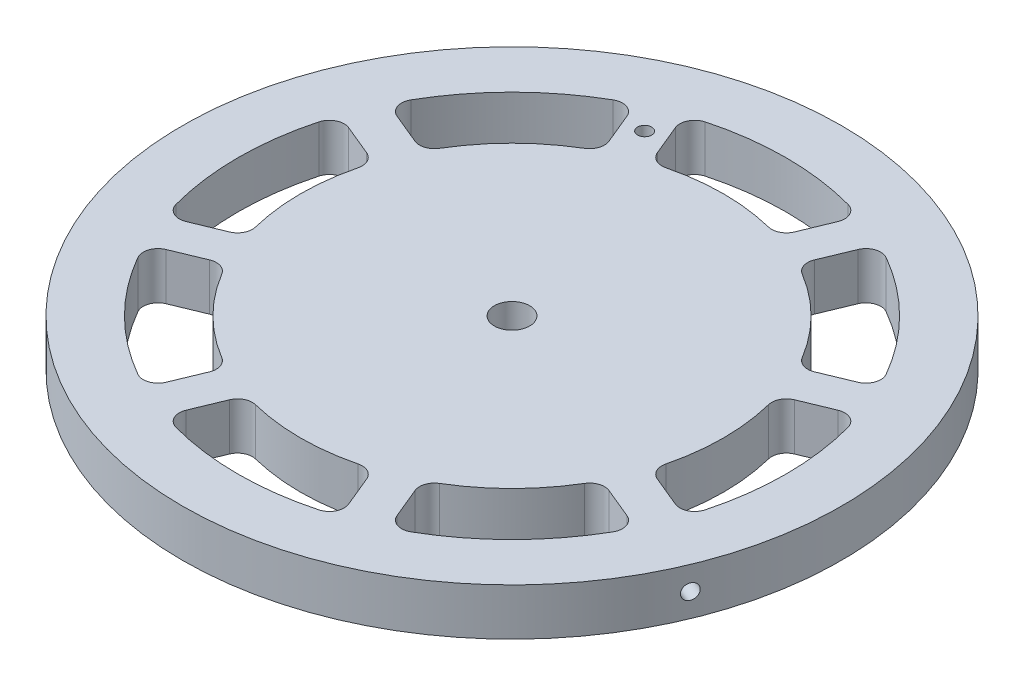
SolidWorks part; units mm, degrees
material "6061-T6 (SS)"
ref_plane "Front Plane" through (0, 0, 0) normal (0, 0, 1) x (1, 0, 0)
ref_plane "Top Plane" through (0, 0, 0) normal (0, 1, 0) x (1, 0, 0)
ref_plane "Right Plane" through (0, 0, 0) normal (1, 0, 0) x (0, 0, -1)
sketch "Sketch2" plane through (0, 0, 0) normal (1, 0, 0) x (0, 0, -1)
  line L0 (0, 0) -> (-89.05, 0)
  line L1 (-89.05, 0) -> (-89.05, 12.7)
  line L2 (-89.05, 12.7) -> (0, 12.7)
  line L5 (0, 12.7) -> (0, 0)
  dimension "D1" = 89.05
  dimension "D2" = 12.7
ref_axis "Axis1" through (0, -0.8888, 0) along (0, 1, 0)
revolve "Revolve1" add sketch "Sketch2" angle 360 about axis through (0, -0.8888, 0) along (0, 1, 0)
hole_wizard "#10-24 Tapped Hole2" positions "Sketch6" profile "Sketch7" tap size "#10-24" standard "ANSI Inch" end condition through all
sketch "Sketch6" plane through (0, 12.7, 0) normal (0, 1, 0) x (1, 0, 0)
  line L0 (0, 0) -> (-53.438, 129.0108) construction
  line L2 (0, 0) -> (0, 109.0908) construction
  point P0 (-25.3336, 61.1608)
  dimension "D1" = 22.5
  dimension "D2" = 66.2
sketch "Sketch7" plane through (-25.3336, 12.7, -61.1608) normal (1, 0, 0) x (0, 0, 1)
  line L0 (0, 0) -> (0, 12.7)
  line L1 (0, 12.7) -> (1.8986, 12.7)
  line L2 (1.8986, 12.7) -> (1.8986, 0)
  line L5 (1.8986, 0) -> (0, 0)
  line L11 (0, -6.35) -> (0, 107.95) construction
  dimension "Thread Major Dia." = 3.7973
  dimension "Thru Tap Drill Depth" = 12.7
sketch "Sketch8" plane through (0, 12.7, 0) normal (0, 1, 0) x (1, 0, 0)
  line L4 (0, 0) -> (0, 93.9995) construction
  line L5 (0, 0) -> (113.8372, 0) construction
  line L6 (-17.1671, 54.5107) -> (-23.6536, 70.1706)
  line L7 (17.1671, 54.5107) -> (23.6536, 70.1706)
  line L8 (0, 0) -> (-25.3336, 61.1608) construction
  arc A0 (-17.1671, 54.5107) -> (17.1671, 54.5107) centre (0, 0) cw
  arc A1 (-23.6536, 70.1706) -> (23.6536, 70.1706) centre (0, 0) cw
  circle A2 centre (0, 0) radius 89.05 construction
  dimension "D1" = 57.15
  dimension "D2" = 15
  dimension "D3" = 5
extrude "Cut-Extrude1" cut sketch "Sketch8" against normal through all
fillet "Fillet1" radius 4 4 edges at (17.1671, 6.35, -54.5107) (23.6536, 6.35, -70.1706) (-17.1671, 6.35, -54.5107) (-23.6536, 6.35, -70.1706)
pattern_circular "CirPattern4" count 8 over 360 about axis through (0, 0, 0) along (0, 1, 0) of "Cut-Extrude1", "Fillet1"
ref_plane "Plane1" through (0, 0, 0) normal (0.9239, 0, 0.3827) x (0, 1, 0)
hole_wizard "#20 (0.161) Diameter Hole1" positions "Sketch16" profile "Sketch15" hole size "#20" standard "ANSI Inch"
sketch "Sketch16" plane through (0, 0, 0) normal (0.9239, 0, 0.3827) x (0, 1, 0)
  point P0 (6.35, 0)
  dimension "D1" = 6.35
sketch "Sketch15" plane through (0, 6.35, 0) normal (0, 1, 0) x (-0.3827, 0, 0.9239)
  line L0 (0, 0) -> (0, 116.3494)
  line L1 (0, 116.3494) -> (2.0447, 116.3494)
  line L2 (2.0447, 116.3494) -> (2.0447, 0)
  line L5 (2.0447, 0) -> (0, 0)
  line L11 (0, -6.35) -> (0, 107.95) construction
  dimension "Thru Hole Dia." = 4.0894
  dimension "Thru Hole Depth" = 116.3494
ref_plane "Plane2" through (34.078, 0, -82.2715) normal (0.3827, 0, -0.9239) x (-0.9239, 0, -0.3827)
sketch "Sketch22" plane through (0, 12.7, 0) normal (0, 1, 0) x (1, 0, 0)
  circle A0 centre (0, 0) radius 4.765
  dimension "D1" = 9.53
extrude "Cut-Extrude4" cut sketch "Sketch22" against normal blind 12.8
equation "\"TubeDiameter\" = 6.500in"
equation "\"D1@Sketch2\"=89.05"
equation "\"D2@Sketch6\"=66.2"
